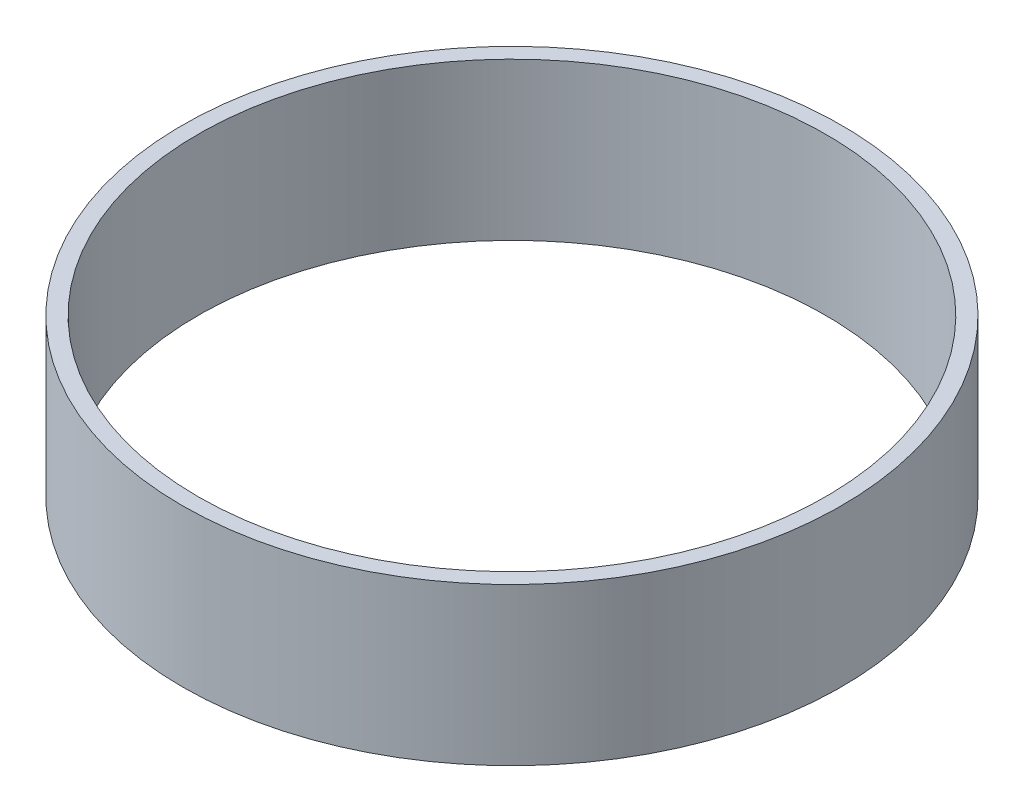
SolidWorks part; units mm, degrees
ref_plane "Front Plane" through (0, 0, 0) normal (0, 0, 1) x (1, 0, 0)
ref_plane "Top Plane" through (0, 0, 0) normal (0, 1, 0) x (1, 0, 0)
ref_plane "Right Plane" through (0, 0, 0) normal (1, 0, 0) x (0, 0, -1)
sketch "Sketch1" plane through (0, 0, 0) normal (0, 1, 0) x (1, 0, 0)
  circle A0 centre (0, 0) radius 20
  circle A1 centre (0, 0) radius 21
  dimension "D1" = 42
  dimension "D2" = 40
extrude "Boss-Extrude1" add sketch "Sketch1" along normal blind 10
